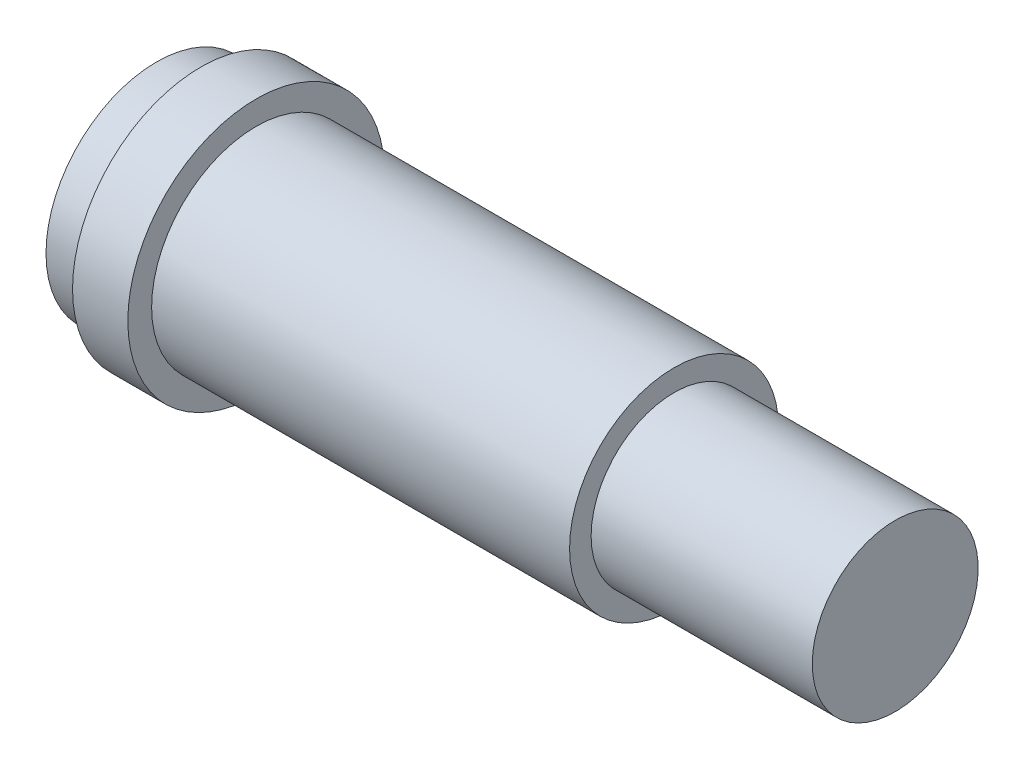
SolidWorks part; units mm, degrees
material "6061-T6 (SS)"
ref_plane "Front Plane" through (0, 0, 0) normal (0, 0, 1) x (1, 0, 0)
ref_plane "Top Plane" through (0, 0, 0) normal (0, 1, 0) x (1, 0, 0)
ref_plane "Right Plane" through (0, 0, 0) normal (1, 0, 0) x (0, 0, -1)
sketch "Sketch1" plane through (0, 0, 0) normal (0, 0, 1) x (1, 0, 0)
  line L0 (-160.1307, 0) -> (7846.4052, 0) construction
  line L1 (-6.35, 0) -> (18.35, 0)
  line L2 (18.35, 0) -> (18.35, 2.3813)
  line L3 (18.35, 2.3813) -> (12, 2.3812)
  line L4 (0, 3) -> (0, 3.683)
  line L5 (0, 3.683) -> (-1.5875, 3.683)
  line L6 (-6.35, 3.175) -> (-6.35, 0)
  line L7 (-1.5875, 3.683) -> (-1.5875, 3.175)
  line L8 (-1.5875, 3.175) -> (-6.35, 3.175)
  line L9 (12, 2.3812) -> (12, 3)
  line L10 (12, 3) -> (0, 3)
  dimension "D1" = 6.35
  dimension "D2" = 6
  dimension "D3" = 0.508
  dimension "D4" = 1.5875
  dimension "D5" = 4.7625
  dimension "D6" = 4.7625
  dimension "D7" = 12
  dimension "D8" = 6.35
revolve "Revolve1" add sketch "Sketch1" angle 360 about L0
extrude "Cut-Extrude1" cut sketch "Sketch2" against normal through all
sketch "Sketch2" plane through (-2.8575, -8.1966, -7.0786) normal (1, 0, 0) x (0, -0.923, -0.3848)
  circle A1 centre (-10.2893, -3.3796) radius 6.35
